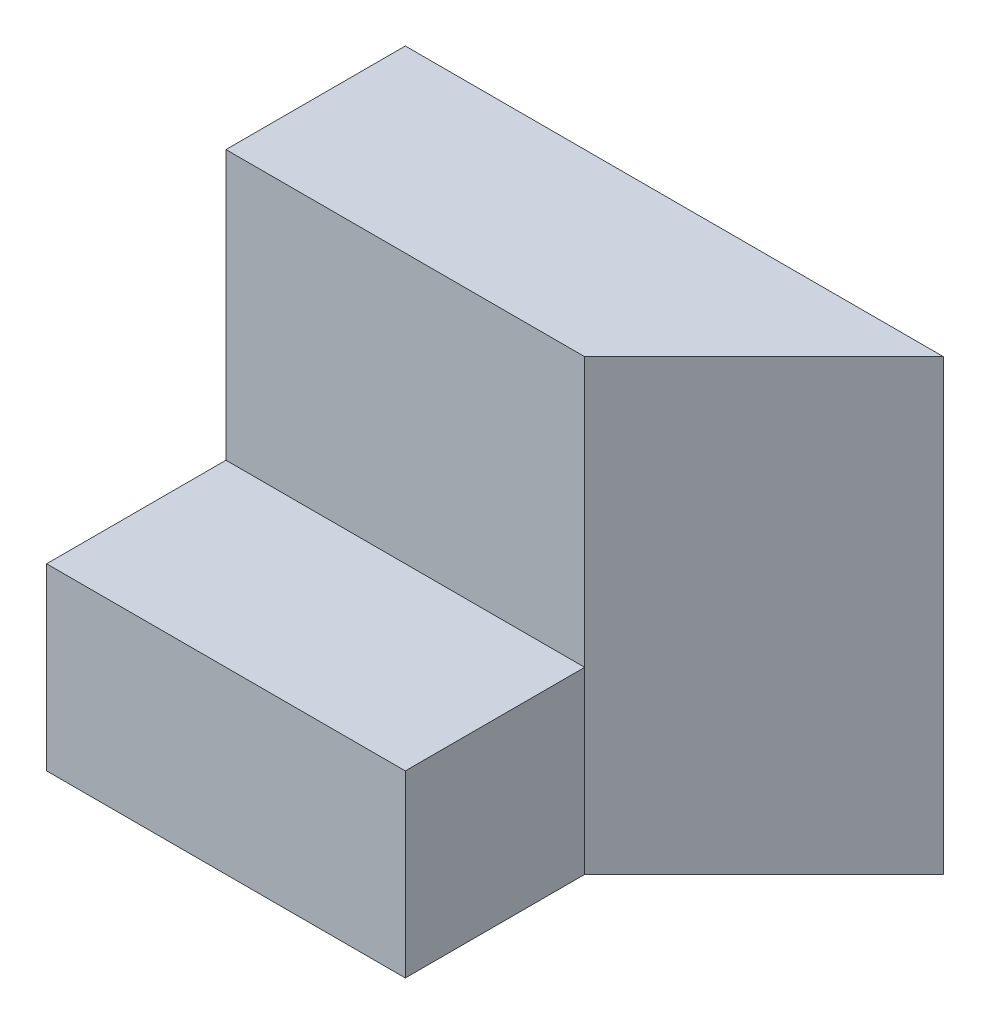
SolidWorks part; units mm, degrees
ref_plane "Front Plane" through (0, 0, 0) normal (0, 0, 1) x (1, 0, 0)
ref_plane "Top Plane" through (0, 0, 0) normal (0, 1, 0) x (1, 0, 0)
ref_plane "Right Plane" through (0, 0, 0) normal (1, 0, 0) x (0, 0, -1)
sketch "Sketch1" plane through (0, 0, 0) normal (0, 1, 0) x (1, 0, 0)
  line L0 (4, 2) -> (4, 0)
  line L1 (0, 0) -> (4, 0)
  line L2 (0, 2) -> (0, 4)
  line L3 (0, 4) -> (6, 4)
  line L4 (6, 4) -> (4, 2)
  line L6 (0, 2) -> (0, 0)
  dimension "D1" = 45
  dimension "D2" = 2
  dimension "D3" = 2
  dimension "D4" = 6
  dimension "D5" = 2
  dimension "D6" = 2
extrude "Boss-Extrude1" add sketch "Sketch1" along normal blind 5
sketch "Sketch4" plane through (0, 0, 0) normal (-1, 0, 0) x (0, 0, 1)
  line L1 (0, 5) -> (-2, 5)
  line L2 (0, 5) -> (0, 2)
  line L3 (0, 2) -> (-2, 2)
  line L4 (-2, 5) -> (-2, 2)
  dimension "D1" = 2
  dimension "D2" = 3
extrude "Cut-Extrude3" cut sketch "Sketch4" against normal blind 15
